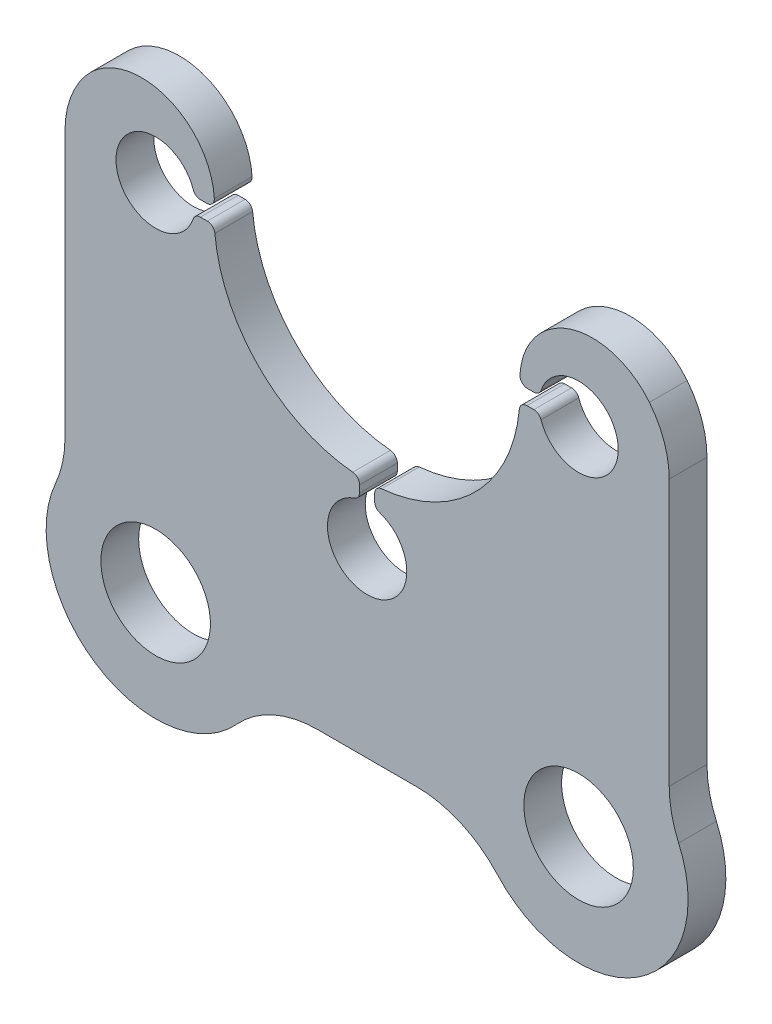
SolidWorks part; units mm, degrees
ref_plane "Plane1" through (0, 0, 0) normal (0, 0, 1) x (1, 0, 0)
ref_plane "Plane2" through (0, 0, 0) normal (0, 1, 0) x (1, 0, 0)
ref_plane "Plane3" through (0, 0, 0) normal (1, 0, 0) x (0, 0, -1)
sketch "Sketch1" plane through (0, 0, 0) normal (0, 0, 1) x (1, 0, 0)
  line L0 (0, 0) -> (28, 0) construction
  line L1 (0, 0) -> (0, -71) construction
  line L2 (0, 0) -> (-28, 0) construction
  line L3 (21.1557, -1) -> (22.0786, -1)
  line L4 (-6.5349, -52) -> (6.5349, -52)
  line L5 (0, 0) -> (-28, 0) construction
  line L6 (21.2295, 1) -> (22.0786, 1)
  line L7 (40, 0) -> (40, -35.2208)
  line L8 (-40, 0) -> (-40, -35.2208)
  line L9 (-21.2295, 1) -> (-22.0786, 1)
  line L10 (-21.1557, -1) -> (-22.0786, -1)
  line L11 (1, -22.0786) -> (1, -21.1557)
  line L12 (-1, -22.0786) -> (-1, -21.1557)
  arc A0 (-20.1601, -1.9059) -> (-1.9059, -20.1601) centre (0, 0) ccw
  arc A1 (-28, 0) -> (28, 0) centre (0, 0) ccw construction
  arc A2 (23.0261, -1.68) -> (23.0261, 1.68) centre (28, 0) ccw
  arc A3 (20.2313, 2.0607) -> (37.3775, 7.4875) centre (29.8483, 1.4758) cw
  arc A4 (41.25, -41.1104) -> (17.2675, -56.75) centre (28, -47) cw
  circle A5 centre (28, -47) radius 7.25
  circle A6 centre (-28, -47) radius 7.25
  arc A7 (-41.25, -41.1104) -> (-17.2675, -56.75) centre (-28, -47) ccw
  arc A8 (21.2295, 1) -> (20.2313, 2.0607) centre (21.2295, 2) cw
  arc A9 (-23.0261, -1.68) -> (-23.0261, 1.68) centre (-28, 0) cw
  arc A10 (-1.68, -23.0261) -> (1.68, -23.0261) centre (0, -28) ccw
  arc A11 (6.5349, -52) -> (17.2675, -56.75) centre (6.5349, -66.5) cw
  arc A12 (-17.2675, -56.75) -> (-6.5349, -52) centre (-6.5349, -66.5) cw
  arc A13 (40, 0) -> (37.3775, 7.4875) centre (28, 0) ccw
  arc A14 (21.1557, -1) -> (20.1601, -1.9059) centre (21.1557, -2) ccw
  arc A15 (22.0786, -1) -> (23.0261, -1.68) centre (22.0786, -2) cw
  arc A16 (22.0786, 1) -> (23.0261, 1.68) centre (22.0786, 2) ccw
  arc A17 (-22.0786, 1) -> (-23.0261, 1.68) centre (-22.0786, 2) cw
  arc A18 (-22.0786, -1) -> (-23.0261, -1.68) centre (-22.0786, -2) ccw
  arc A19 (-21.1557, -1) -> (-20.1601, -1.9059) centre (-21.1557, -2) cw
  arc A20 (-40, 0) -> (-37.3775, 7.4875) centre (-28, 0) cw
  arc A21 (-21.2295, 1) -> (-20.2313, 2.0607) centre (-21.2295, 2) ccw
  arc A22 (-20.2313, 2.0607) -> (-37.3775, 7.4875) centre (-29.8483, 1.4758) ccw
  arc A23 (1.9059, -20.1601) -> (20.1601, -1.9059) centre (0, 0) ccw
  arc A24 (1, -21.1557) -> (1.9059, -20.1601) centre (2, -21.1557) cw
  arc A25 (-1, -21.1557) -> (-1.9059, -20.1601) centre (-2, -21.1557) ccw
  arc A26 (-1, -22.0786) -> (-1.68, -23.0261) centre (-2, -22.0786) cw
  arc A27 (1, -22.0786) -> (1.68, -23.0261) centre (2, -22.0786) ccw
  arc A28 (-41.25, -41.1104) -> (-40, -35.2208) centre (-54.5, -35.2208) ccw
  arc A29 (41.25, -41.1104) -> (40, -35.2208) centre (54.5, -35.2208) cw
  point P31 (14.3893, -52)
  point P33 (20.2253, 1)
  point P36 (20.2253, -1)
  point P39 (22.8461, -1)
  point P42 (22.8461, 1)
  point P60 (1, -20.2253)
  point P63 (-1, -20.2253)
  point P66 (-1, -22.8461)
  point P69 (1, -22.8461)
  point P73 (-14.3893, -52)
  dimension "D1" = 14.5
  dimension "D2" = 10.5
  dimension "D3" = 56
  dimension "D4" = 14.5
  dimension "D5" = 28
  dimension "D6" = 20.25
  dimension "D7" = 2
  dimension "D9" = 80
  dimension "D10" = 1
  dimension "D12" = 1
  dimension "D14" = 14.5
  dimension "D13" = 5
  dimension "D8" = 47
  dimension "D11" = 2
extrude "Extrude1" add sketch "Sketch1" along normal blind 5
